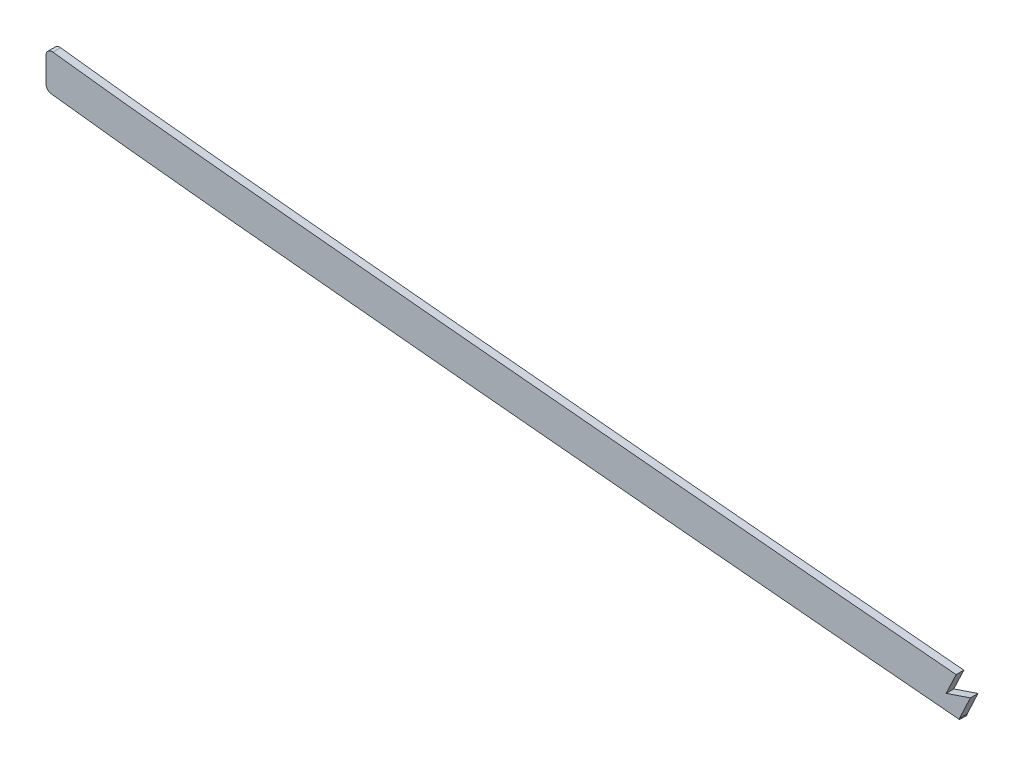
SolidWorks part; units mm, degrees
ref_plane "Front Plane" through (0, 0, 0) normal (0, 0, 1) x (1, 0, 0)
ref_plane "Top Plane" through (0, 0, 0) normal (0, 1, 0) x (1, 0, 0)
ref_plane "Right Plane" through (0, 0, 0) normal (1, 0, 0) x (0, 0, -1)
sketch "Sketch2" plane through (0, 0, 0) normal (0, 0, 1) x (1, 0, 0)
  line L0 (0, 0) -> (266.9553, 0) construction
  line L1 (825.5, 263.7287) -> (825.5, 174.6622)
  line L2 (2491.74, 117.5472) -> (2491.74, 52.664)
  spline S0 degree 5 poles (818.067, 264.7065) (827.0431, 263.4992) (836.0291, 262.3734) (845.0868, 261.3058) (891.3865, 256.087) (937.6862, 251.7792) (973.4521, 248.2277) (1071.9467, 239.0511) (1170.4413, 229.7315) (1231.7919, 224.5039) (1324.8993, 216.7906) (1418.0067, 209.0401) (1449.7429, 206.3618) (1636.9286, 190.5211) (1824.1143, 175.4092) (1979.9669, 164.2997) (2156.2686, 150.4144) (2332.5703, 133.8572) (2354.213, 131.7851) (2436.3555, 123.724) (2518.4981, 114.8591) (2579.4813, 107.7425) (2639.6368, 100.3834) (2699.7923, 92.6045) knots 77.930822 77.930822 77.930822 77.930822 77.930822 77.930822 82.465793 82.465793 82.465793 100.79329 100.79329 100.79329 131.098954 131.098954 131.098954 146.769198 146.769198 146.769198 223.533959 223.533959 223.533959 233.943117 233.943117 233.943117 264.216209 264.216209 264.216209 264.216209 264.216209 264.216209 weights 1 1 1 1 1 1 1 1 1 1 1 1 1 1 1 1 1 1 1 1 1 1 1 1
  spline S1 degree 1 poles (816.0355, 249.6025) (2697.8379, 77.4903) knots 0 0 1 1 construction
  spline S2 degree 3 poles (816.0355, 249.6025) (820.896, 248.9488) (830.6112, 247.6997) (845.2811, 245.9534) (860.0865, 244.2956) (879.8307, 242.1866) (904.37, 239.6983) (933.571, 236.8322) (962.6427, 234.0237) (991.7626, 231.242) (1021.072, 228.4759) (1060.3764, 224.797) (1109.513, 220.1844) (1168.5112, 214.8171) (1227.5001, 209.6621) (1306.1332, 203.0212) (1404.3615, 194.9207) (1522.2399, 184.9181) (1640.1829, 175.167) (1758.1654, 165.7576) (1876.1554, 156.5909) (1994.0875, 147.4533) (2092.2687, 139.6242) (2170.748, 133.0797) (2219.7717, 128.8422) (2258.984, 125.3472) (2288.3795, 122.6709) (2317.8122, 119.9317) (2347.5515, 117.1004) (2377.1599, 114.2101) (2406.4697, 111.269) (2435.8183, 108.2401) (2474.9139, 104.0902) (2523.7162, 98.6933) (2582.0419, 91.9123) (2640.0752, 84.8576) (2678.5742, 79.9814) (2697.8379, 77.4903) knots 77.930822 77.930822 77.930822 77.930822 79.386176 80.841531 82.296885 83.75224 86.662949 89.573658 92.484367 95.395077 98.305786 101.216495 107.037913 112.859332 118.68075 124.502168 136.145005 147.787842 159.430678 171.073515 182.716352 194.359189 206.002025 211.823444 217.644862 220.555571 223.46628 226.37699 229.287699 232.198408 235.109117 238.019826 240.930535 246.751954 252.573372 258.39479 264.216209 264.216209 264.216209 264.216209
  spline S3 degree 5 poles (818.067, -264.7065) (827.0431, -263.4992) (836.0291, -262.3734) (845.0868, -261.3058) (891.3865, -256.087) (937.6862, -251.7792) (973.4521, -248.2277) (1071.9467, -239.0511) (1170.4413, -229.7315) (1231.7919, -224.5039) (1324.8993, -216.7906) (1418.0067, -209.0401) (1449.7429, -206.3618) (1636.9286, -190.5211) (1824.1143, -175.4092) (1979.9669, -164.2997) (2156.2686, -150.4144) (2332.5703, -133.8572) (2354.213, -131.7851) (2436.3555, -123.724) (2518.4981, -114.8591) (2579.4813, -107.7425) (2639.6368, -100.3834) (2699.7923, -92.6045) knots 77.930822 77.930822 77.930822 77.930822 77.930822 77.930822 82.465793 82.465793 82.465793 100.79329 100.79329 100.79329 131.098954 131.098954 131.098954 146.769198 146.769198 146.769198 223.533959 223.533959 223.533959 233.943117 233.943117 233.943117 264.216209 264.216209 264.216209 264.216209 264.216209 264.216209 weights 1 1 1 1 1 1 1 1 1 1 1 1 1 1 1 1 1 1 1 1 1 1 1 1
  point P2 (0, 0)
  dimension "D1" = 818.067
  dimension "D2" = 825.5
  dimension "D3" = 2491.74
  dimension "D4" = 15.24
extrude "Boss-Extrude1" add sketch "Sketch2" along normal mid plane 3.175 contours L1 S2 L2 S0
fillet "Fillet1" radius 2.54 4 edges at (2491.74, 102.2148, 0) (825.5, 248.3644, 0)
sketch "Sketch3" plane through (0, 0, 1.5875) normal (0, 0, 1) x (1, 0, 0)
  line L0 (1201.6419, 227.2278) -> (1201.6419, 233.6579)
  line L1 (1201.6419, 227.2278) -> (1197.5086, 218.4497)
  line L2 (1197.5086, 218.4497) -> (1207.4958, 221.815)
  line L3 (1207.4958, 221.815) -> (1203.045, 212.262)
  line L10 (1201.6419, 233.6579) -> (2527.6669, 125.8675)
  line L11 (2527.6669, 125.8675) -> (2495.3756, 68.8828)
  line L12 (2495.3756, 68.8828) -> (1203.045, 209.5285)
  line L13 (1203.045, 209.5285) -> (1203.045, 212.262)
  spline S0 degree 5 poles (828.3591, 263.3639) (835.3006, 262.485) (842.2713, 261.6451) (849.2939, 260.8336) (893.49, 255.8914) (937.6862, 251.7793) (973.4521, 248.2278) (1071.9467, 239.0512) (1170.4413, 229.7316) (1231.792, 224.504) (1324.8993, 216.7907) (1418.0067, 209.0402) (1449.7429, 206.3619) (1636.9286, 190.5212) (1824.1143, 175.4092) (1979.967, 164.2997) (2156.2686, 150.4145) (2332.5703, 133.8572) (2354.213, 131.7851) (2393.888, 127.8915) (2433.5631, 123.8105) (2452.2167, 121.8477) (2470.8575, 119.8423) (2489.4775, 117.7961) knots 78.969534 78.969534 78.969534 78.969534 78.969534 78.969534 82.465793 82.465793 82.465793 100.79329 100.79329 100.79329 131.098954 131.098954 131.098954 146.769198 146.769198 146.769198 223.533959 223.533959 223.533959 233.943117 233.943117 233.943117 243.183575 243.183575 243.183575 243.183575 243.183575 243.183575 weights 1 1 1 1 1 1 1 1 1 1 1 1 1 1 1 1 1 1 1 1 1 1 1 1 construction
extrude "Cut-Extrude1" cut sketch "Sketch3" against normal blind 7.62
